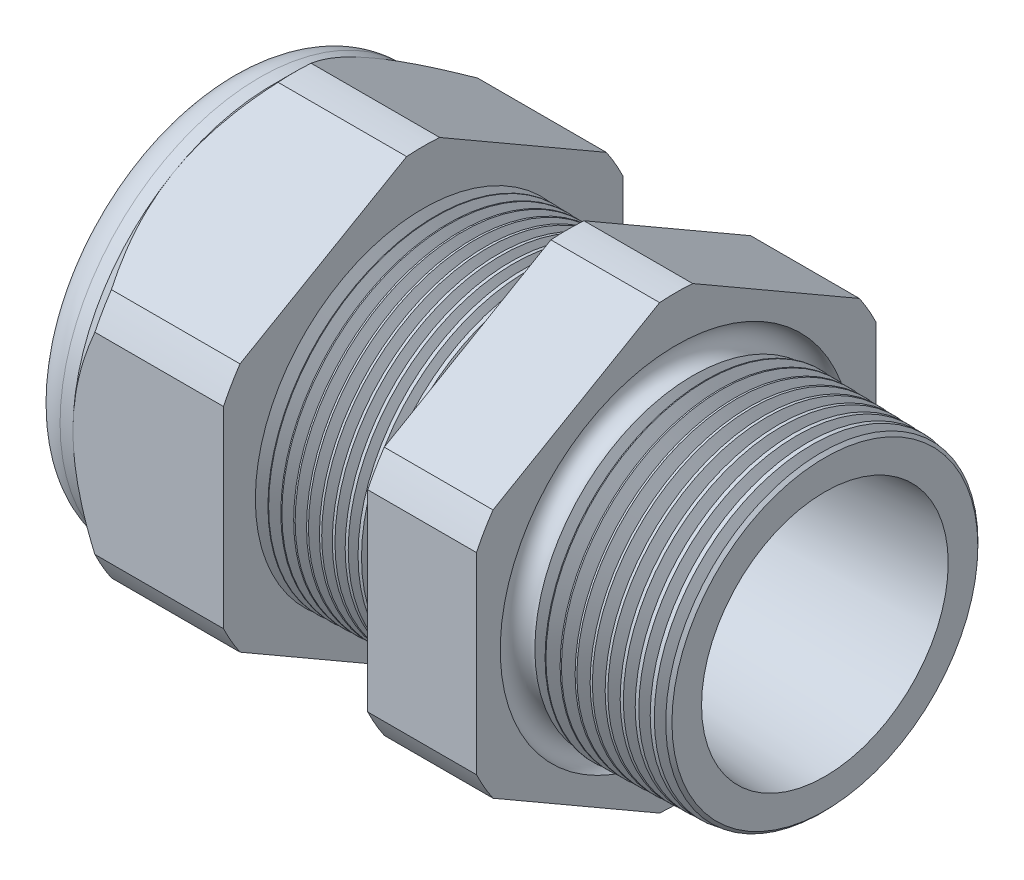
SolidWorks part; units mm, degrees
ref_plane "Front Plane" through (0, 0, 0) normal (0, 0, 1) x (1, 0, 0)
ref_plane "Top Plane" through (0, 0, 0) normal (0, 1, 0) x (1, 0, 0)
ref_plane "Right Plane" through (0, 0, 0) normal (1, 0, 0) x (0, 0, -1)
sketch "Sketch10" plane through (0, 0, 0) normal (0, 0, 1) x (1, 0, 0)
  line L0 (0, 0) -> (-115.3565, 0) construction
  line L1 (-34.798, 5.969) -> (-22.998, 5.969)
  line L2 (1.016, 7.3722) -> (1.016, 9.4042)
  line L3 (-7.874, 9.637) -> (1.016, 9.4042)
  line L4 (-7.874, 23.876) -> (-7.874, 9.637)
  line L5 (-7.874, 23.876) -> (-14.374, 23.876)
  line L6 (-14.374, 23.876) -> (-14.374, 9.8072)
  line L7 (-22.998, 10.033) -> (-14.374, 9.8072)
  line L8 (-22.998, 10.033) -> (-22.998, 23.876)
  line L9 (-22.998, 23.876) -> (-31.998, 23.876)
  line L10 (-31.998, 23.876) -> (-31.998, 11.938)
  line L11 (-31.998, 11.938) -> (-34.798, 11.938)
  line L12 (-34.798, 11.938) -> (-34.798, 5.969)
  line L13 (-22.998, 5.969) -> (1.016, 7.3722)
  dimension "D1" = 35.814
  dimension "D2" = 11.938
  dimension "D3" = 1.5
  dimension "D4" = 2.032
  dimension "A" = 20.066
  dimension "D6" = 23.876
  dimension "D8" = 47.752
  dimension "D9" = 2.8
  dimension "D10" = 9
  dimension "D11" = 6.5
  dimension "D" = 8.89
revolve "Revolve2" add sketch "Sketch10" angle 360 about L0
sketch "Sketch12" plane through (-31.998, 0, 0) normal (-1, 0, 0) x (0, 0, 1)
  line L1 (-0.9882, 13.2143) -> (-10.9498, 7.4629)
  line L2 (-11.938, 5.7513) -> (-11.938, -5.7513)
  line L3 (-10.9498, -7.4629) -> (-0.9882, -13.2143)
  line L4 (0.9882, -13.2143) -> (10.9498, -7.4629)
  line L5 (11.938, -5.7513) -> (11.938, 5.7513)
  line L6 (10.9498, 7.4629) -> (0.9882, 13.2143)
  circle A0 centre (0, 0) radius 11.938 construction
  arc A1 (0.9882, 13.2143) -> (-0.9882, 13.2143) centre (0, 0) ccw
  arc A2 (-10.9498, 7.4629) -> (-11.938, 5.7513) centre (0, 0) ccw
  arc A3 (-11.938, -5.7513) -> (-10.9498, -7.4629) centre (0, 0) ccw
  arc A4 (-0.9882, -13.2143) -> (0.9882, -13.2143) centre (0, 0) ccw
  arc A5 (10.9498, -7.4629) -> (11.938, -5.7513) centre (0, 0) ccw
  arc A6 (11.938, 5.7513) -> (10.9498, 7.4629) centre (0, 0) ccw
  dimension "D2" = 26.5024
  dimension "D1" = 23.876
extrude "Cut-Extrude2" cut sketch "Sketch12" against normal through all flip side to cut
fillet "Fillet4" radius 2.032 1 edges at (-34.798, 0, -11.938)
sketch "Sketch19" plane through (-31.998, 0, 0) normal (-1, 0, 0) x (0, 0, 1)
  line L0 (11.938, 0) -> (11.938, 5.7513) construction
  circle A0 centre (0, 0) radius 11.938
extrude "Cut-Extrude3" cut sketch "Sketch19" against normal blind 2 draft 45 flip side to cut
chamfer "Chamfer1" distance 0.254 angle 45 1 edges at (1.016, 0, -9.4042)
sketch "Sketch21" plane through (-34.798, 0, 0) normal (-1, 0, 0) x (0, 0, 1)
  circle A0 centre (0, 0) radius 5.969
  circle A2 centre (0, 0) radius 5.969 construction
extrude "plug" add sketch "Sketch21" against normal blind 6.35 separate body
sketch "Sketch22" plane through (-34.798, 0, 0) normal (-1, 0, 0) x (0, 0, 1)
  circle A0 centre (0, 0) radius 5.715
  circle A1 centre (0, 0) radius 5.969 construction
  dimension "D1" = 0.254
extrude "Cut-Extrude4" cut sketch "Sketch22" against normal blind 0.508
sketch "Sketch27" plane through (-34.29, 0, 0) normal (-1, 0, 0) x (0, 0, 1)
  line L0 (-4.3624, 0) -> (4.3624, 0) construction
  circle A0 centre (-4.1849, 0) radius 1.524
  circle A1 centre (0, 0) radius 5.715 construction
  dimension "D1" = 0.0061
  dimension "holedia" = 3.048
extrude "plugholes" cut sketch "Sketch27" against normal through all
pattern_circular "CirPattern1" count 3 over 360 about axis through (0, 0, 0) along (1, 0, 0) of "plugholes"
sketch "Sketch28" [suppressed] plane through (-29.464, 0, 0) normal (-1, 0, 0) x (0, 0, 1)
  circle A0 centre (0, 0) radius 0.762
  dimension "midholedia" = 3.048
extrude "midhole" [suppressed] cut sketch "Sketch28" against normal through all
sketch "Sketch29" plane through (0, 0, 0) normal (0, 0, 1) x (1, 0, 0)
  line L0 (-22.998, 10.033) -> (-22.265, 10.0138)
  line L1 (-14.374, 9.8072) -> (-22.998, 10.033) construction
  line L2 (-22.265, 10.0138) -> (-22.6481, 9.3886)
  line L3 (-22.6481, 9.3886) -> (-22.998, 10.033)
  dimension "D1" = 60
  dimension "D2" = 60
  dimension "D3" = 0.635
revolve "Cut-Revolve1" cut sketch "Sketch29" angle 360 about axis through (0, 0, 0) along (-1, 0, 0)
pattern_linear "LPattern1" count 11 spacing 0.762 along (1, 0, 0) of "Cut-Revolve1"
sketch "Sketch30" plane through (0, 0, 0) normal (0, 0, 1) x (1, 0, 0)
  line L0 (-7.874, 9.637) -> (-6.9944, 9.6139)
  line L1 (-7.874, 13.2143) -> (-7.874, 7.4629) construction
  line L2 (0.7621, 9.4108) -> (-7.874, 9.637) construction
  line L3 (-6.9944, 9.6139) -> (-7.4542, 8.8637)
  line L4 (-7.4542, 8.8637) -> (-7.874, 9.637)
  dimension "D1" = 60
  dimension "D2" = 60
  dimension "D3" = 0.762
revolve "Cut-Revolve2" cut sketch "Sketch30" angle 360 about axis through (0, 0, 0) along (-1, 0, 0)
pattern_linear "LPattern2" count 10 spacing 0.889 along (1, 0, 0) of "Cut-Revolve2"
sketch "Sketch31" [suppressed] plane through (-38.354, 0, 0) normal (-1, 0, 0) x (0, 0, 1)
  line L0 (-1.905, 1.905) -> (1.905, 1.905)
  line L1 (-1.905, -1.905) -> (1.905, -1.905)
  circle A0 centre (0, 0) radius 1.905 construction
  arc A1 (-1.905, 1.905) -> (-1.905, -1.905) centre (-1.905, 0) ccw
  arc A2 (1.905, 1.905) -> (1.905, -1.905) centre (1.905, 0) cw
extrude "Cut-Extrude5" [suppressed] cut sketch "Sketch31" against normal through all
sketch "Sketch32" plane through (0, 0, 0) normal (0, 0, 1) x (1, 0, 0)
  line L0 (-7.874, 13.2143) -> (-7.874, 7.4629) construction
  circle A0 centre (-7.747, 9.637) radius 0.889
  dimension "D2" = 1.778
  dimension "D1" = 0.127
revolve "Cut-Revolve3" cut sketch "Sketch32" angle 360 about axis through (0, 0, 0) along (-1, 0, 0)
